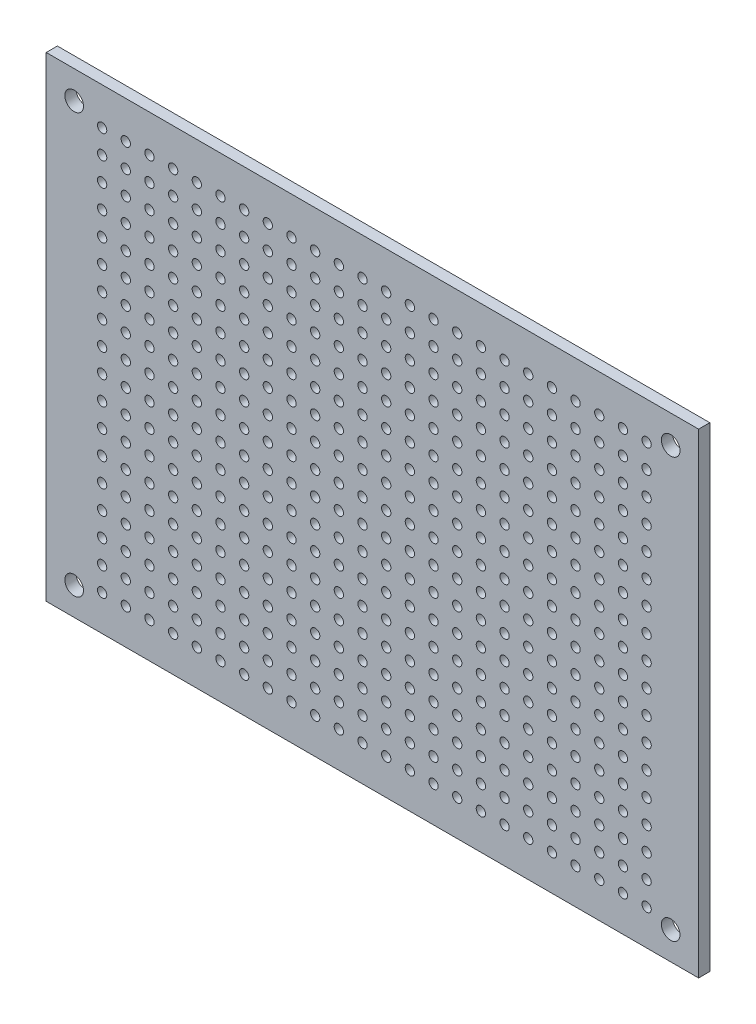
SolidWorks part; units mm, degrees
material "Ст 3 ГОСТ 380-88"
ref_plane "FRONT" through (0, 0, 0) normal (0, 0, 1) x (1, 0, 0)
ref_plane "TOP" through (0, 0, 0) normal (0, 1, 0) x (1, 0, 0)
ref_plane "RIGHT" through (0, 0, 0) normal (1, 0, 0) x (0, 0, -1)
sketch "Эскиз1" plane through (0, 0, 0) normal (0, 0, 1) x (1, 0, 0)
  line L0 (35, 51) -> (35, 0) construction
  line L1 (0, 0) -> (70, 0)
  line L2 (0, 0) -> (0, 51)
  line L3 (0, 51) -> (70, 51)
  line L4 (70, 0) -> (70, 51)
  line L5 (70, 25.5) -> (0, 25.5) construction
  line L6 (6, 47) -> (64.42, 47) construction
  line L7 (6, 47) -> (6, 3.82) construction
  circle A0 centre (6, 47) radius 0.5
  circle A1 centre (3, 48) radius 1
  circle A2 centre (67, 48) radius 1
  circle A3 centre (67, 3) radius 1
  circle A4 centre (3, 3) radius 1
  circle A5 centre (8.54, 47) radius 0.5
  circle A6 centre (11.08, 47) radius 0.5
  circle A7 centre (13.62, 47) radius 0.5
  circle A8 centre (16.16, 47) radius 0.5
  circle A9 centre (18.7, 47) radius 0.5
  circle A10 centre (21.24, 47) radius 0.5
  circle A11 centre (23.78, 47) radius 0.5
  circle A12 centre (26.32, 47) radius 0.5
  circle A13 centre (28.86, 47) radius 0.5
  circle A14 centre (31.4, 47) radius 0.5
  circle A15 centre (33.94, 47) radius 0.5
  circle A16 centre (36.48, 47) radius 0.5
  circle A17 centre (39.02, 47) radius 0.5
  circle A18 centre (41.56, 47) radius 0.5
  circle A19 centre (44.1, 47) radius 0.5
  circle A20 centre (46.64, 47) radius 0.5
  circle A21 centre (49.18, 47) radius 0.5
  circle A22 centre (51.72, 47) radius 0.5
  circle A23 centre (54.26, 47) radius 0.5
  circle A24 centre (56.8, 47) radius 0.5
  circle A25 centre (59.34, 47) radius 0.5
  circle A26 centre (61.88, 47) radius 0.5
  circle A27 centre (64.42, 47) radius 0.5
  circle A28 centre (8.54, 44.46) radius 0.5
  circle A29 centre (11.08, 44.46) radius 0.5
  circle A30 centre (13.62, 44.46) radius 0.5
  circle A31 centre (16.16, 44.46) radius 0.5
  circle A32 centre (18.7, 44.46) radius 0.5
  circle A33 centre (21.24, 44.46) radius 0.5
  circle A34 centre (23.78, 44.46) radius 0.5
  circle A35 centre (26.32, 44.46) radius 0.5
  circle A36 centre (28.86, 44.46) radius 0.5
  circle A37 centre (31.4, 44.46) radius 0.5
  circle A38 centre (33.94, 44.46) radius 0.5
  circle A39 centre (36.48, 44.46) radius 0.5
  circle A40 centre (39.02, 44.46) radius 0.5
  circle A41 centre (41.56, 44.46) radius 0.5
  circle A42 centre (44.1, 44.46) radius 0.5
  circle A43 centre (46.64, 44.46) radius 0.5
  circle A44 centre (49.18, 44.46) radius 0.5
  circle A45 centre (51.72, 44.46) radius 0.5
  circle A46 centre (54.26, 44.46) radius 0.5
  circle A47 centre (56.8, 44.46) radius 0.5
  circle A48 centre (59.34, 44.46) radius 0.5
  circle A49 centre (61.88, 44.46) radius 0.5
  circle A50 centre (64.42, 44.46) radius 0.5
  circle A51 centre (8.54, 41.92) radius 0.5
  circle A52 centre (11.08, 41.92) radius 0.5
  circle A53 centre (13.62, 41.92) radius 0.5
  circle A54 centre (16.16, 41.92) radius 0.5
  circle A55 centre (18.7, 41.92) radius 0.5
  circle A56 centre (21.24, 41.92) radius 0.5
  circle A57 centre (23.78, 41.92) radius 0.5
  circle A58 centre (26.32, 41.92) radius 0.5
  circle A59 centre (28.86, 41.92) radius 0.5
  circle A60 centre (31.4, 41.92) radius 0.5
  circle A61 centre (33.94, 41.92) radius 0.5
  circle A62 centre (36.48, 41.92) radius 0.5
  circle A63 centre (39.02, 41.92) radius 0.5
  circle A64 centre (41.56, 41.92) radius 0.5
  circle A65 centre (44.1, 41.92) radius 0.5
  circle A66 centre (46.64, 41.92) radius 0.5
  circle A67 centre (49.18, 41.92) radius 0.5
  circle A68 centre (51.72, 41.92) radius 0.5
  circle A69 centre (54.26, 41.92) radius 0.5
  circle A70 centre (56.8, 41.92) radius 0.5
  circle A71 centre (59.34, 41.92) radius 0.5
  circle A72 centre (61.88, 41.92) radius 0.5
  circle A73 centre (64.42, 41.92) radius 0.5
  circle A74 centre (8.54, 39.38) radius 0.5
  circle A75 centre (11.08, 39.38) radius 0.5
  circle A76 centre (13.62, 39.38) radius 0.5
  circle A77 centre (16.16, 39.38) radius 0.5
  circle A78 centre (18.7, 39.38) radius 0.5
  circle A79 centre (21.24, 39.38) radius 0.5
  circle A80 centre (23.78, 39.38) radius 0.5
  circle A81 centre (26.32, 39.38) radius 0.5
  circle A82 centre (28.86, 39.38) radius 0.5
  circle A83 centre (31.4, 39.38) radius 0.5
  circle A84 centre (33.94, 39.38) radius 0.5
  circle A85 centre (36.48, 39.38) radius 0.5
  circle A86 centre (39.02, 39.38) radius 0.5
  circle A87 centre (41.56, 39.38) radius 0.5
  circle A88 centre (44.1, 39.38) radius 0.5
  circle A89 centre (46.64, 39.38) radius 0.5
  circle A90 centre (49.18, 39.38) radius 0.5
  circle A91 centre (51.72, 39.38) radius 0.5
  circle A92 centre (54.26, 39.38) radius 0.5
  circle A93 centre (56.8, 39.38) radius 0.5
  circle A94 centre (59.34, 39.38) radius 0.5
  circle A95 centre (61.88, 39.38) radius 0.5
  circle A96 centre (64.42, 39.38) radius 0.5
  circle A97 centre (8.54, 36.84) radius 0.5
  circle A98 centre (11.08, 36.84) radius 0.5
  circle A99 centre (13.62, 36.84) radius 0.5
  circle A100 centre (16.16, 36.84) radius 0.5
  circle A101 centre (18.7, 36.84) radius 0.5
  circle A102 centre (21.24, 36.84) radius 0.5
  circle A103 centre (23.78, 36.84) radius 0.5
  circle A104 centre (26.32, 36.84) radius 0.5
  circle A105 centre (28.86, 36.84) radius 0.5
  circle A106 centre (31.4, 36.84) radius 0.5
  circle A107 centre (33.94, 36.84) radius 0.5
  circle A108 centre (36.48, 36.84) radius 0.5
  circle A109 centre (39.02, 36.84) radius 0.5
  circle A110 centre (41.56, 36.84) radius 0.5
  circle A111 centre (44.1, 36.84) radius 0.5
  circle A112 centre (46.64, 36.84) radius 0.5
  circle A113 centre (49.18, 36.84) radius 0.5
  circle A114 centre (51.72, 36.84) radius 0.5
  circle A115 centre (54.26, 36.84) radius 0.5
  circle A116 centre (56.8, 36.84) radius 0.5
  circle A117 centre (59.34, 36.84) radius 0.5
  circle A118 centre (61.88, 36.84) radius 0.5
  circle A119 centre (64.42, 36.84) radius 0.5
  circle A120 centre (8.54, 34.3) radius 0.5
  circle A121 centre (11.08, 34.3) radius 0.5
  circle A122 centre (13.62, 34.3) radius 0.5
  circle A123 centre (16.16, 34.3) radius 0.5
  circle A124 centre (18.7, 34.3) radius 0.5
  circle A125 centre (21.24, 34.3) radius 0.5
  circle A126 centre (23.78, 34.3) radius 0.5
  circle A127 centre (26.32, 34.3) radius 0.5
  circle A128 centre (28.86, 34.3) radius 0.5
  circle A129 centre (31.4, 34.3) radius 0.5
  circle A130 centre (33.94, 34.3) radius 0.5
  circle A131 centre (36.48, 34.3) radius 0.5
  circle A132 centre (39.02, 34.3) radius 0.5
  circle A133 centre (41.56, 34.3) radius 0.5
  circle A134 centre (44.1, 34.3) radius 0.5
  circle A135 centre (46.64, 34.3) radius 0.5
  circle A136 centre (49.18, 34.3) radius 0.5
  circle A137 centre (51.72, 34.3) radius 0.5
  circle A138 centre (54.26, 34.3) radius 0.5
  circle A139 centre (56.8, 34.3) radius 0.5
  circle A140 centre (59.34, 34.3) radius 0.5
  circle A141 centre (61.88, 34.3) radius 0.5
  circle A142 centre (64.42, 34.3) radius 0.5
  circle A143 centre (8.54, 31.76) radius 0.5
  circle A144 centre (11.08, 31.76) radius 0.5
  circle A145 centre (13.62, 31.76) radius 0.5
  circle A146 centre (16.16, 31.76) radius 0.5
  circle A147 centre (18.7, 31.76) radius 0.5
  circle A148 centre (21.24, 31.76) radius 0.5
  circle A149 centre (23.78, 31.76) radius 0.5
  circle A150 centre (26.32, 31.76) radius 0.5
  circle A151 centre (28.86, 31.76) radius 0.5
  circle A152 centre (31.4, 31.76) radius 0.5
  circle A153 centre (33.94, 31.76) radius 0.5
  circle A154 centre (36.48, 31.76) radius 0.5
  circle A155 centre (39.02, 31.76) radius 0.5
  circle A156 centre (41.56, 31.76) radius 0.5
  circle A157 centre (44.1, 31.76) radius 0.5
  circle A158 centre (46.64, 31.76) radius 0.5
  circle A159 centre (49.18, 31.76) radius 0.5
  circle A160 centre (51.72, 31.76) radius 0.5
  circle A161 centre (54.26, 31.76) radius 0.5
  circle A162 centre (56.8, 31.76) radius 0.5
  circle A163 centre (59.34, 31.76) radius 0.5
  circle A164 centre (61.88, 31.76) radius 0.5
  circle A165 centre (64.42, 31.76) radius 0.5
  circle A166 centre (8.54, 29.22) radius 0.5
  circle A167 centre (11.08, 29.22) radius 0.5
  circle A168 centre (13.62, 29.22) radius 0.5
  circle A169 centre (16.16, 29.22) radius 0.5
  circle A170 centre (18.7, 29.22) radius 0.5
  circle A171 centre (21.24, 29.22) radius 0.5
  circle A172 centre (23.78, 29.22) radius 0.5
  circle A173 centre (26.32, 29.22) radius 0.5
  circle A174 centre (28.86, 29.22) radius 0.5
  circle A175 centre (31.4, 29.22) radius 0.5
  circle A176 centre (33.94, 29.22) radius 0.5
  circle A177 centre (36.48, 29.22) radius 0.5
  circle A178 centre (39.02, 29.22) radius 0.5
  circle A179 centre (41.56, 29.22) radius 0.5
  circle A180 centre (44.1, 29.22) radius 0.5
  circle A181 centre (46.64, 29.22) radius 0.5
  circle A182 centre (49.18, 29.22) radius 0.5
  circle A183 centre (51.72, 29.22) radius 0.5
  circle A184 centre (54.26, 29.22) radius 0.5
  circle A185 centre (56.8, 29.22) radius 0.5
  circle A186 centre (59.34, 29.22) radius 0.5
  circle A187 centre (61.88, 29.22) radius 0.5
  circle A188 centre (64.42, 29.22) radius 0.5
  circle A189 centre (8.54, 26.68) radius 0.5
  circle A190 centre (11.08, 26.68) radius 0.5
  circle A191 centre (13.62, 26.68) radius 0.5
  circle A192 centre (16.16, 26.68) radius 0.5
  circle A193 centre (18.7, 26.68) radius 0.5
  circle A194 centre (21.24, 26.68) radius 0.5
  circle A195 centre (23.78, 26.68) radius 0.5
  circle A196 centre (26.32, 26.68) radius 0.5
  circle A197 centre (28.86, 26.68) radius 0.5
  circle A198 centre (31.4, 26.68) radius 0.5
  circle A199 centre (33.94, 26.68) radius 0.5
  circle A200 centre (36.48, 26.68) radius 0.5
  circle A201 centre (39.02, 26.68) radius 0.5
  circle A202 centre (41.56, 26.68) radius 0.5
  circle A203 centre (44.1, 26.68) radius 0.5
  circle A204 centre (46.64, 26.68) radius 0.5
  circle A205 centre (49.18, 26.68) radius 0.5
  circle A206 centre (51.72, 26.68) radius 0.5
  circle A207 centre (54.26, 26.68) radius 0.5
  circle A208 centre (56.8, 26.68) radius 0.5
  circle A209 centre (59.34, 26.68) radius 0.5
  circle A210 centre (61.88, 26.68) radius 0.5
  circle A211 centre (64.42, 26.68) radius 0.5
  circle A212 centre (8.54, 24.14) radius 0.5
  circle A213 centre (11.08, 24.14) radius 0.5
  circle A214 centre (13.62, 24.14) radius 0.5
  circle A215 centre (16.16, 24.14) radius 0.5
  circle A216 centre (18.7, 24.14) radius 0.5
  circle A217 centre (21.24, 24.14) radius 0.5
  circle A218 centre (23.78, 24.14) radius 0.5
  circle A219 centre (26.32, 24.14) radius 0.5
  circle A220 centre (28.86, 24.14) radius 0.5
  circle A221 centre (31.4, 24.14) radius 0.5
  circle A222 centre (33.94, 24.14) radius 0.5
  circle A223 centre (36.48, 24.14) radius 0.5
  circle A224 centre (39.02, 24.14) radius 0.5
  circle A225 centre (41.56, 24.14) radius 0.5
  circle A226 centre (44.1, 24.14) radius 0.5
  circle A227 centre (46.64, 24.14) radius 0.5
  circle A228 centre (49.18, 24.14) radius 0.5
  circle A229 centre (51.72, 24.14) radius 0.5
  circle A230 centre (54.26, 24.14) radius 0.5
  circle A231 centre (56.8, 24.14) radius 0.5
  circle A232 centre (59.34, 24.14) radius 0.5
  circle A233 centre (61.88, 24.14) radius 0.5
  circle A234 centre (64.42, 24.14) radius 0.5
  circle A235 centre (8.54, 21.6) radius 0.5
  circle A236 centre (11.08, 21.6) radius 0.5
  circle A237 centre (13.62, 21.6) radius 0.5
  circle A238 centre (16.16, 21.6) radius 0.5
  circle A239 centre (18.7, 21.6) radius 0.5
  circle A240 centre (21.24, 21.6) radius 0.5
  circle A241 centre (23.78, 21.6) radius 0.5
  circle A242 centre (26.32, 21.6) radius 0.5
  circle A243 centre (28.86, 21.6) radius 0.5
  circle A244 centre (31.4, 21.6) radius 0.5
  circle A245 centre (33.94, 21.6) radius 0.5
  circle A246 centre (36.48, 21.6) radius 0.5
  circle A247 centre (39.02, 21.6) radius 0.5
  circle A248 centre (41.56, 21.6) radius 0.5
  circle A249 centre (44.1, 21.6) radius 0.5
  circle A250 centre (46.64, 21.6) radius 0.5
  circle A251 centre (49.18, 21.6) radius 0.5
  circle A252 centre (51.72, 21.6) radius 0.5
  circle A253 centre (54.26, 21.6) radius 0.5
  circle A254 centre (56.8, 21.6) radius 0.5
  circle A255 centre (59.34, 21.6) radius 0.5
  circle A256 centre (61.88, 21.6) radius 0.5
  circle A257 centre (64.42, 21.6) radius 0.5
  circle A258 centre (8.54, 19.06) radius 0.5
  circle A259 centre (11.08, 19.06) radius 0.5
  circle A260 centre (13.62, 19.06) radius 0.5
  circle A261 centre (16.16, 19.06) radius 0.5
  circle A262 centre (18.7, 19.06) radius 0.5
  circle A263 centre (21.24, 19.06) radius 0.5
  circle A264 centre (23.78, 19.06) radius 0.5
  circle A265 centre (26.32, 19.06) radius 0.5
  circle A266 centre (28.86, 19.06) radius 0.5
  circle A267 centre (31.4, 19.06) radius 0.5
  circle A268 centre (33.94, 19.06) radius 0.5
  circle A269 centre (36.48, 19.06) radius 0.5
  circle A270 centre (39.02, 19.06) radius 0.5
  circle A271 centre (41.56, 19.06) radius 0.5
  circle A272 centre (44.1, 19.06) radius 0.5
  circle A273 centre (46.64, 19.06) radius 0.5
  circle A274 centre (49.18, 19.06) radius 0.5
  circle A275 centre (51.72, 19.06) radius 0.5
  circle A276 centre (54.26, 19.06) radius 0.5
  circle A277 centre (56.8, 19.06) radius 0.5
  circle A278 centre (59.34, 19.06) radius 0.5
  circle A279 centre (61.88, 19.06) radius 0.5
  circle A280 centre (64.42, 19.06) radius 0.5
  circle A281 centre (8.54, 16.52) radius 0.5
  circle A282 centre (11.08, 16.52) radius 0.5
  circle A283 centre (13.62, 16.52) radius 0.5
  circle A284 centre (16.16, 16.52) radius 0.5
  circle A285 centre (18.7, 16.52) radius 0.5
  circle A286 centre (21.24, 16.52) radius 0.5
  circle A287 centre (23.78, 16.52) radius 0.5
  circle A288 centre (26.32, 16.52) radius 0.5
  circle A289 centre (28.86, 16.52) radius 0.5
  circle A290 centre (31.4, 16.52) radius 0.5
  circle A291 centre (33.94, 16.52) radius 0.5
  circle A292 centre (36.48, 16.52) radius 0.5
  circle A293 centre (39.02, 16.52) radius 0.5
  circle A294 centre (41.56, 16.52) radius 0.5
  circle A295 centre (44.1, 16.52) radius 0.5
  circle A296 centre (46.64, 16.52) radius 0.5
  circle A297 centre (49.18, 16.52) radius 0.5
  circle A298 centre (51.72, 16.52) radius 0.5
  circle A299 centre (54.26, 16.52) radius 0.5
  circle A300 centre (56.8, 16.52) radius 0.5
  circle A301 centre (59.34, 16.52) radius 0.5
  circle A302 centre (61.88, 16.52) radius 0.5
  circle A303 centre (64.42, 16.52) radius 0.5
  circle A304 centre (8.54, 13.98) radius 0.5
  circle A305 centre (11.08, 13.98) radius 0.5
  circle A306 centre (13.62, 13.98) radius 0.5
  circle A307 centre (16.16, 13.98) radius 0.5
  circle A308 centre (18.7, 13.98) radius 0.5
  circle A309 centre (21.24, 13.98) radius 0.5
  circle A310 centre (23.78, 13.98) radius 0.5
  circle A311 centre (26.32, 13.98) radius 0.5
  circle A312 centre (28.86, 13.98) radius 0.5
  circle A313 centre (31.4, 13.98) radius 0.5
  circle A314 centre (33.94, 13.98) radius 0.5
  circle A315 centre (36.48, 13.98) radius 0.5
  circle A316 centre (39.02, 13.98) radius 0.5
  circle A317 centre (41.56, 13.98) radius 0.5
  circle A318 centre (44.1, 13.98) radius 0.5
  circle A319 centre (46.64, 13.98) radius 0.5
  circle A320 centre (49.18, 13.98) radius 0.5
  circle A321 centre (51.72, 13.98) radius 0.5
  circle A322 centre (54.26, 13.98) radius 0.5
  circle A323 centre (56.8, 13.98) radius 0.5
  circle A324 centre (59.34, 13.98) radius 0.5
  circle A325 centre (61.88, 13.98) radius 0.5
  circle A326 centre (64.42, 13.98) radius 0.5
  circle A327 centre (8.54, 11.44) radius 0.5
  circle A328 centre (11.08, 11.44) radius 0.5
  circle A329 centre (13.62, 11.44) radius 0.5
  circle A330 centre (16.16, 11.44) radius 0.5
  circle A331 centre (18.7, 11.44) radius 0.5
  circle A332 centre (21.24, 11.44) radius 0.5
  circle A333 centre (23.78, 11.44) radius 0.5
  circle A334 centre (26.32, 11.44) radius 0.5
  circle A335 centre (28.86, 11.44) radius 0.5
  circle A336 centre (31.4, 11.44) radius 0.5
  circle A337 centre (33.94, 11.44) radius 0.5
  circle A338 centre (36.48, 11.44) radius 0.5
  circle A339 centre (39.02, 11.44) radius 0.5
  circle A340 centre (41.56, 11.44) radius 0.5
  circle A341 centre (44.1, 11.44) radius 0.5
  circle A342 centre (46.64, 11.44) radius 0.5
  circle A343 centre (49.18, 11.44) radius 0.5
  circle A344 centre (51.72, 11.44) radius 0.5
  circle A345 centre (54.26, 11.44) radius 0.5
  circle A346 centre (56.8, 11.44) radius 0.5
  circle A347 centre (59.34, 11.44) radius 0.5
  circle A348 centre (61.88, 11.44) radius 0.5
  circle A349 centre (64.42, 11.44) radius 0.5
  circle A350 centre (8.54, 8.9) radius 0.5
  circle A351 centre (11.08, 8.9) radius 0.5
  circle A352 centre (13.62, 8.9) radius 0.5
  circle A353 centre (16.16, 8.9) radius 0.5
  circle A354 centre (18.7, 8.9) radius 0.5
  circle A355 centre (21.24, 8.9) radius 0.5
  circle A356 centre (23.78, 8.9) radius 0.5
  circle A357 centre (26.32, 8.9) radius 0.5
  circle A358 centre (28.86, 8.9) radius 0.5
  circle A359 centre (31.4, 8.9) radius 0.5
  circle A360 centre (33.94, 8.9) radius 0.5
  circle A361 centre (36.48, 8.9) radius 0.5
  circle A362 centre (39.02, 8.9) radius 0.5
  circle A363 centre (41.56, 8.9) radius 0.5
  circle A364 centre (44.1, 8.9) radius 0.5
  circle A365 centre (46.64, 8.9) radius 0.5
  circle A366 centre (49.18, 8.9) radius 0.5
  circle A367 centre (51.72, 8.9) radius 0.5
  circle A368 centre (54.26, 8.9) radius 0.5
  circle A369 centre (56.8, 8.9) radius 0.5
  circle A370 centre (59.34, 8.9) radius 0.5
  circle A371 centre (61.88, 8.9) radius 0.5
  circle A372 centre (64.42, 8.9) radius 0.5
  circle A373 centre (8.54, 6.36) radius 0.5
  circle A374 centre (11.08, 6.36) radius 0.5
  circle A375 centre (13.62, 6.36) radius 0.5
  circle A376 centre (16.16, 6.36) radius 0.5
  circle A377 centre (18.7, 6.36) radius 0.5
  circle A378 centre (21.24, 6.36) radius 0.5
  circle A379 centre (23.78, 6.36) radius 0.5
  circle A380 centre (26.32, 6.36) radius 0.5
  circle A381 centre (28.86, 6.36) radius 0.5
  circle A382 centre (31.4, 6.36) radius 0.5
  circle A383 centre (33.94, 6.36) radius 0.5
  circle A384 centre (36.48, 6.36) radius 0.5
  circle A385 centre (39.02, 6.36) radius 0.5
  circle A386 centre (41.56, 6.36) radius 0.5
  circle A387 centre (44.1, 6.36) radius 0.5
  circle A388 centre (46.64, 6.36) radius 0.5
  circle A389 centre (49.18, 6.36) radius 0.5
  circle A390 centre (51.72, 6.36) radius 0.5
  circle A391 centre (54.26, 6.36) radius 0.5
  circle A392 centre (56.8, 6.36) radius 0.5
  circle A393 centre (59.34, 6.36) radius 0.5
  circle A394 centre (61.88, 6.36) radius 0.5
  circle A395 centre (64.42, 6.36) radius 0.5
  circle A396 centre (8.54, 3.82) radius 0.5
  circle A397 centre (11.08, 3.82) radius 0.5
  circle A398 centre (13.62, 3.82) radius 0.5
  circle A399 centre (16.16, 3.82) radius 0.5
  circle A400 centre (18.7, 3.82) radius 0.5
  circle A401 centre (21.24, 3.82) radius 0.5
  circle A402 centre (23.78, 3.82) radius 0.5
  circle A403 centre (26.32, 3.82) radius 0.5
  circle A404 centre (28.86, 3.82) radius 0.5
  circle A405 centre (31.4, 3.82) radius 0.5
  circle A406 centre (33.94, 3.82) radius 0.5
  circle A407 centre (36.48, 3.82) radius 0.5
  circle A408 centre (39.02, 3.82) radius 0.5
  circle A409 centre (41.56, 3.82) radius 0.5
  circle A410 centre (44.1, 3.82) radius 0.5
  circle A411 centre (46.64, 3.82) radius 0.5
  circle A412 centre (49.18, 3.82) radius 0.5
  circle A413 centre (51.72, 3.82) radius 0.5
  circle A414 centre (54.26, 3.82) radius 0.5
  circle A415 centre (56.8, 3.82) radius 0.5
  circle A416 centre (59.34, 3.82) radius 0.5
  circle A417 centre (61.88, 3.82) radius 0.5
  circle A418 centre (64.42, 3.82) radius 0.5
  circle A419 centre (6, 44.46) radius 0.5
  circle A420 centre (6, 41.92) radius 0.5
  circle A421 centre (6, 39.38) radius 0.5
  circle A422 centre (6, 36.84) radius 0.5
  circle A423 centre (6, 34.3) radius 0.5
  circle A424 centre (6, 31.76) radius 0.5
  circle A425 centre (6, 29.22) radius 0.5
  circle A426 centre (6, 26.68) radius 0.5
  circle A427 centre (6, 24.14) radius 0.5
  circle A428 centre (6, 21.6) radius 0.5
  circle A429 centre (6, 19.06) radius 0.5
  circle A430 centre (6, 16.52) radius 0.5
  circle A431 centre (6, 13.98) radius 0.5
  circle A432 centre (6, 11.44) radius 0.5
  circle A433 centre (6, 8.9) radius 0.5
  circle A434 centre (6, 6.36) radius 0.5
  circle A435 centre (6, 3.82) radius 0.5
  dimension "D3" = 1
  dimension "D4" = 4
  dimension "D5" = 6
  dimension "D6" = 3
  dimension "D7" = 3
  dimension "D8" = 2
  dimension "D9" = 64
  dimension "D10" = 45
  dimension "D13" = 2.54
  dimension "D14" = 2.54
  dimension "D1" = 70
  dimension "D2" = 51
  dimension "D11" = 24
  dimension "D12" = 18
extrude "Бобышка-Вытянуть1" add sketch "Эскиз1" along normal blind 1.2
sketch "Эскиз2" plane through (0, 0, 1.2) normal (0, 0, 1) x (1, 0, 0)
  line L1 (6, 47) -> (64.42, 47)
  line L2 (6, 47) -> (6, 3.82)
  line L3 (6, 3.82) -> (64.42, 3.82)
  line L4 (64.42, 47) -> (64.42, 3.82)
extrude "Вырез-Вытянуть-Тонкостенный1" [suppressed] cut sketch "Эскиз2" against normal blind 0.1 thin
sketch "Эскиз3" plane through (0, 0, 1.2) normal (0, 0, 1) x (1, 0, 0)
  line L0 (13.62, 47) -> (13.62, 3.82)
  line L1 (23.78, 3.82) -> (23.78, 47)
  line L2 (33.94, 47) -> (33.94, 3.82)
  line L3 (44.1, 3.82) -> (44.1, 47)
  line L4 (54.26, 47) -> (54.26, 3.82)
  line L5 (6, 34.3) -> (64.42, 34.3)
  line L6 (6, 24.14) -> (64.42, 24.14)
  line L7 (6, 13.98) -> (64.42, 13.98)
extrude "Вырез-Вытянуть-Тонкостенный2" [suppressed] cut sketch "Эскиз3" against normal blind 0.1 thin
sketch "Эскиз4" plane through (0, 0, 1.2) normal (0, 0, 1) x (1, 0, 0)
  line L0 (4.9874, 47.6456) -> (65.2677, 47.6456) construction
  line L1 (4.9874, 0.2403) -> (65.2677, 0.2403) construction
  line L3 (67.2067, 45.3105) -> (67.2067, 2.8617) construction
  line L4 (1.5401, 45.3105) -> (1.5401, 2.8617) construction
  text T0 "01 02 03 04 05 06 07 08 09 10 11 12 13 14 15 16 17 18 19 20 21 22 23 24" font "@Arial Unicode MS" height 1.5
  text T1 "01 02 03 04 05 06 07 08 09 10 11 12 13 14 15 16 17 18 19 20 21 22 23 24" font "@Arial Unicode MS" height 1.5
  text T2 "<r90>A B C D E F G H I J K L M N O P Q</r>" font "@Arial Unicode MS" height 1.5
  text T3 "<r90>A B C D E F G H I J K L M N O P Q</r>" font "@Arial Unicode MS" height 1.5
extrude "Вырез-Вытянуть1" [suppressed] cut sketch "Эскиз4" against normal blind 0.1
